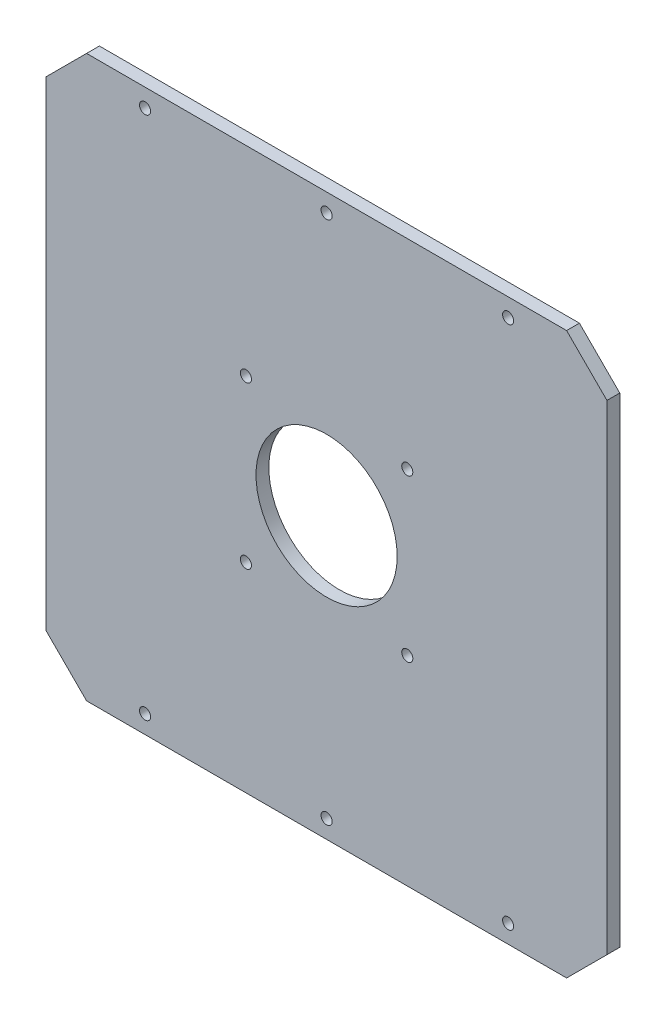
SolidWorks part; units mm, degrees
ref_plane "Front Plane" through (0, 0, 0) normal (0, 0, 1) x (1, 0, 0)
ref_plane "Top Plane" through (0, 0, 0) normal (0, 1, 0) x (1, 0, 0)
ref_plane "Right Plane" through (0, 0, 0) normal (1, 0, 0) x (0, 0, -1)
sketch "Sketch1" plane through (0, 0, 0) normal (0, 0, 1) x (1, 0, 0)
  line L0 (-79.0045, 0) -> (94.053, 0) construction
  line L1 (0, 67.0127) -> (0, -68.6587) construction
  line L3 (139, -139) -> (-139, -139)
  line L4 (139, -139) -> (139, 139)
  line L5 (139, 139) -> (-139, 139)
  line L6 (-139, -139) -> (-139, 139)
  line L7 (139, -139) -> (-139, 139) construction
  line L8 (139, 139) -> (-139, -139) construction
  point P4 (0, 0)
  dimension "D1" = 278
  dimension "D2" = 278
extrude "Boss-Extrude1" add sketch "Sketch1" along normal blind 6.35
sketch "Sketch2" plane through (0, 0, 6.35) normal (0, 0, 1) x (1, 0, 0)
  line L0 (-156.6091, 0) -> (177.3719, 0) construction
  line L1 (0, 110.6274) -> (0, -105.2428) construction
  circle A0 centre (0, 0) radius 35
  circle A1 centre (-40, 40) radius 2.75
  circle A2 centre (40, 40) radius 2.75
  circle A3 centre (40, -40) radius 2.75
  circle A4 centre (-40, -40) radius 2.75
  dimension "D1" = 40
  dimension "D2" = 5.5
  dimension "D3" = 70
  dimension "D4" = 40
extrude "Cut-Extrude1" cut sketch "Sketch2" against normal through all
chamfer "Chamfer1" distance 20 angle 45 4 edges at (139, -139, 3.175) (139, 139, 3.175) (-139, 139, 3.175) (-139, -139, 3.175)
sketch "Sketch4" plane through (0, 0, 6.35) normal (0, 0, 1) x (1, 0, 0)
  line L0 (0, 186.846) -> (0, -174.5938) construction
  line L1 (219.7737, 0) -> (-232.7917, 0) construction
  line L2 (119, 139) -> (-119, 139) construction
  line L3 (-90, -130) -> (0, -130) construction
  circle A0 centre (-90, 130) radius 2.75
  circle A1 centre (0, 130) radius 2.75
  circle A2 centre (90, 130) radius 2.75
  circle A3 centre (90, -130) radius 2.75
  circle A4 centre (0, -130) radius 2.75
  circle A5 centre (-90, -130) radius 2.75
  dimension "D1" = 5.5
  dimension "D2" = 9
  dimension "D3" = 90
extrude "Cut-Extrude2" cut sketch "Sketch4" against normal blind 76.2
equation "\"plate_thickness\" = 6.35 'thickness of the plate "
equation "\"height\"= 180"
equation "\"D1@Boss-Extrude1\"=\"plate_thickness\""
equation "\"t_height\" = 200"
equation "\"t_width\" = 240"
equation "\"t_length\" = 240"
equation "\"plate_spacing\" = 1"
equation "\"front_plate_height\" = \"t_height\" + 38"
equation "\"front_plate_width\" = \"t_width\" + 38"
equation "\"side_plate_height\" = \"front_plate_height\""
equation "\"side_plate_length\" = \"t_length\" + 38"
equation "\"top_plate_width\" = \"front_plate_width\""
equation "\"top_plate_length\" = \"side_plate_length\""
equation "\"D2@Sketch1\"=\"top_plate_width\""
equation "\"D1@Sketch1\"=\"top_plate_length\""
equation "\"plate_hole_spacing\"= 9"
equation "\"connector_D1\" = 70 'the big holes diameter"
equation "\"connector_mtg_D2\"= 5.5 'mounting holes"
equation "\"mtg_dfc\" = 40 'mounting hole distance from center"
equation "\"D3@Sketch2\"=\"connector_D1\""
equation "\"D2@Sketch2\"=\"mtg_hole_D\""
equation "\"D4@Sketch2\"=\"mtg_dfc\""
equation "\"D1@Sketch2\"=\"mtg_dfc\""
equation "\"mtg_hole_D\" = 5.5 'mounting holes"
equation "\"plate_hole_from_edge\" = 9"
equation "\"D1@Sketch4\"=\"mtg_hole_D\""
equation "\"D2@Sketch4\"=\"plate_hole_from_edge\""
